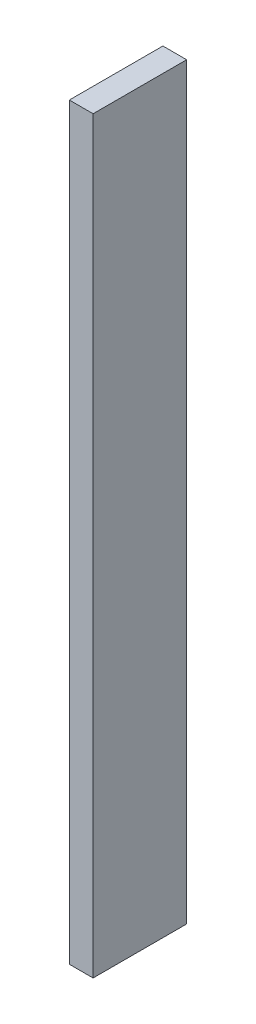
SolidWorks part; units mm, degrees
ref_plane "Front Plane" through (0, 0, 0) normal (0, 0, 1) x (1, 0, 0)
ref_plane "Top Plane" through (0, 0, 0) normal (0, 1, 0) x (1, 0, 0)
ref_plane "Right Plane" through (0, 0, 0) normal (1, 0, 0) x (0, 0, -1)
sketch "Sketch1" plane through (0, 0, 0) normal (1, 0, 0) x (0, 0, -1)
  line L1 (-25, 200) -> (25, 200)
  line L2 (-25, 200) -> (-25, -200)
  line L3 (-25, -200) -> (25, -200)
  line L4 (25, 200) -> (25, -200)
  line L5 (-25, 200) -> (25, -200) construction
  line L6 (-25, -200) -> (25, 200) construction
  point P0 (0, 0)
  dimension "D1" = 50
  dimension "D2" = 400
extrude "Boss-Extrude1" add sketch "Sketch1" along normal blind 12.7
equation "\"width\"= 50mm"
equation "\"Length\" = 400mm"
equation "\"D2@Sketch1\"=\"Length\""
equation "\"D1@Sketch1\"=\"width\""
